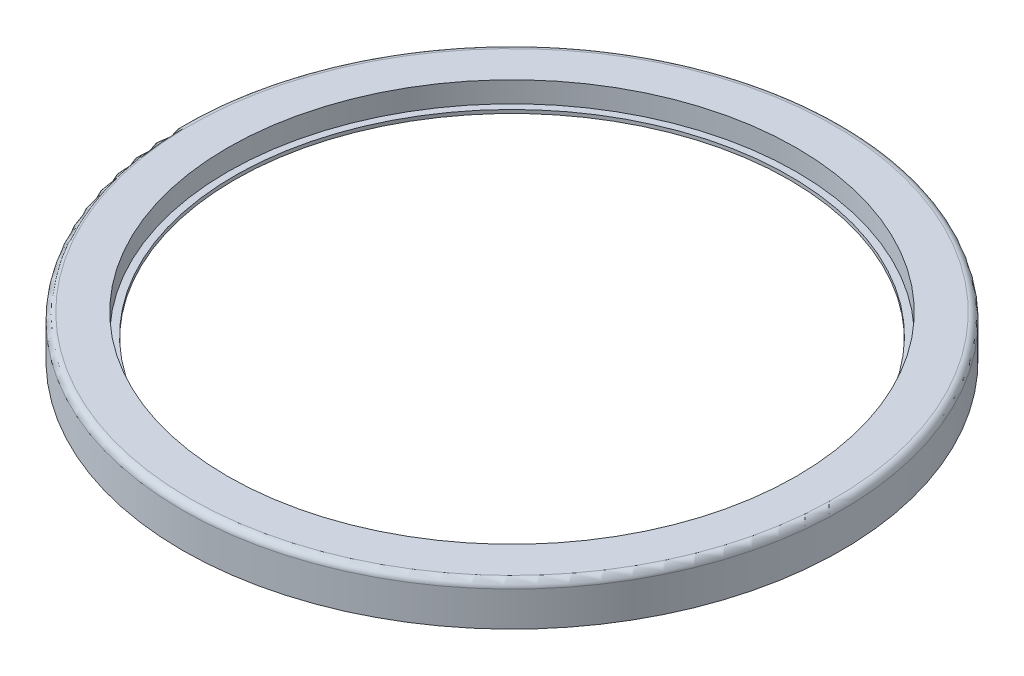
SolidWorks part; units mm, degrees
ref_plane "Front Plane" through (0, 0, 0) normal (0, 0, 1) x (1, 0, 0)
ref_plane "Top Plane" through (0, 0, 0) normal (0, 1, 0) x (1, 0, 0)
ref_plane "Right Plane" through (0, 0, 0) normal (1, 0, 0) x (0, 0, -1)
sketch "Sketch1" plane through (0, 0, 0) normal (0, 1, 0) x (1, 0, 0)
  circle A0 centre (0, 0) radius 47.5
  dimension "D1" = 95
extrude "Boss-Extrude1" add sketch "Sketch1" along normal blind 2
sketch "Sketch2" plane through (0, 0, 0) normal (0, -1, 0) x (1, 0, 0)
  circle A0 centre (0, 0) radius 42.25
  dimension "D1" = 84.5
extrude "Boss-Extrude2" add sketch "Sketch2" along normal blind 1.5 draft 2
sketch "Sketch5" plane through (0, 2, 0) normal (0, 1, 0) x (1, 0, 0)
  circle A0 centre (0, 0) radius 10
extrude "Cut-Extrude1" cut sketch "Sketch5" against normal blind 4
chamfer "Chamfer1" distance 1 angle 45 2 edges at (0, -1.5, -10) (0, 2, 10)
sketch "Sketch7" plane through (0, 0, 0) normal (0, -1, 0) x (1, 0, 0)
  circle A0 centre (0, 0) radius 47.5
  circle A1 centre (0, 0) radius 45.7
  circle A3 centre (0, 0) radius 47.5 construction
  dimension "D1" = 1.8
extrude "Boss-Extrude3" add sketch "Sketch7" along normal blind 4
fillet "Fillet2" radius 1 1 edges at (0, 2, 47.5)
sketch "Sketch8" plane through (0, 2, 0) normal (0, 1, 0) x (1, 0, 0)
  circle A0 centre (0, 0) radius 41
  dimension "D1" = 82
extrude "Cut-Extrude4" cut sketch "Sketch8" against normal blind 3
sketch "Sketch9" plane through (0, -1, 0) normal (0, 1, 0) x (1, 0, 0)
  circle A0 centre (0, 0) radius 40
extrude "Cut-Extrude5" cut sketch "Sketch9" against normal blind 5
sketch "Sketch10" plane through (0, -4, 0) normal (0, -1, 0) x (1, 0, 0)
  circle A0 centre (0, 0) radius 45.7
  circle A1 centre (0, 0) radius 45.2
  circle A2 centre (0, 0) radius 45.7 construction
  dimension "D1" = 0.5
extrude "Boss-Extrude4" add sketch "Sketch10" against normal blind 1.5
